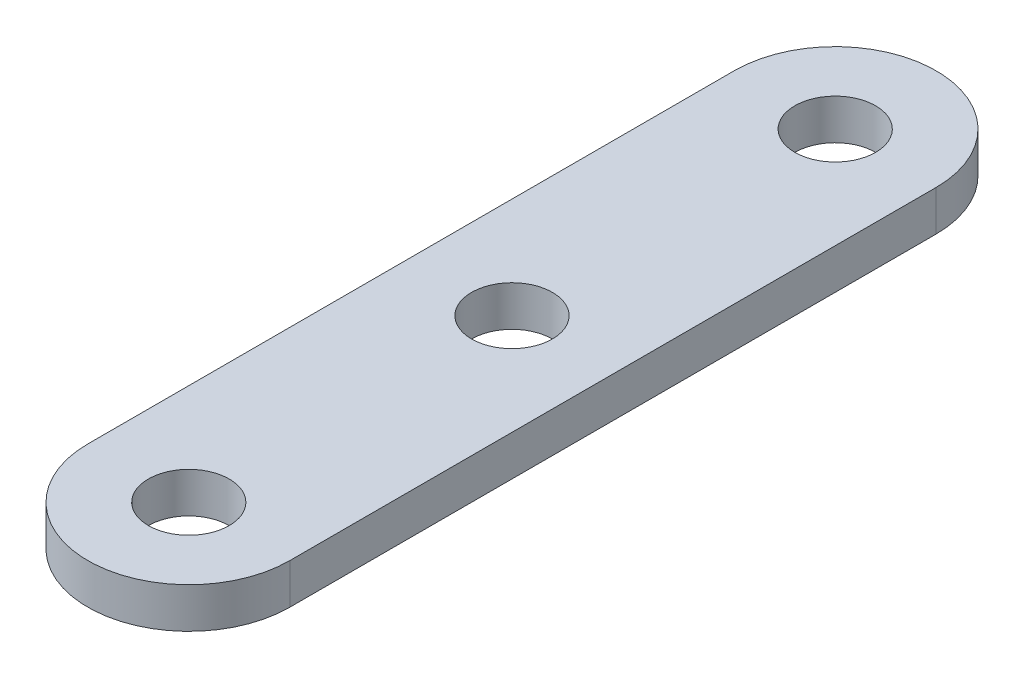
SolidWorks part; units mm, degrees
ref_plane "Front Plane" through (0, 0, 0) normal (0, 0, 1) x (1, 0, 0)
ref_plane "Top Plane" through (0, 0, 0) normal (0, 1, 0) x (1, 0, 0)
ref_plane "Right Plane" through (0, 0, 0) normal (1, 0, 0) x (0, 0, -1)
sketch "Sketch1" plane through (0, 0, 0) normal (0, 1, 0) x (1, 0, 0)
  line L0 (0, 0) -> (0, 50.8) construction
  line L1 (-7.9375, 50.8) -> (-7.9375, 0)
  line L2 (7.9375, 50.8) -> (7.9375, 0)
  circle A0 centre (0, 0) radius 3.175
  circle A1 centre (0, 0) radius 7.9375
  circle A2 centre (0, 50.8) radius 3.175
  circle A3 centre (0, 50.8) radius 7.9375
  circle A4 centre (0, 25.4) radius 3.175
  circle A5 centre (0, 25.4) radius 7.9375
extrude "Boss-Extrude1" add sketch "Sketch1" along normal blind 3.175
